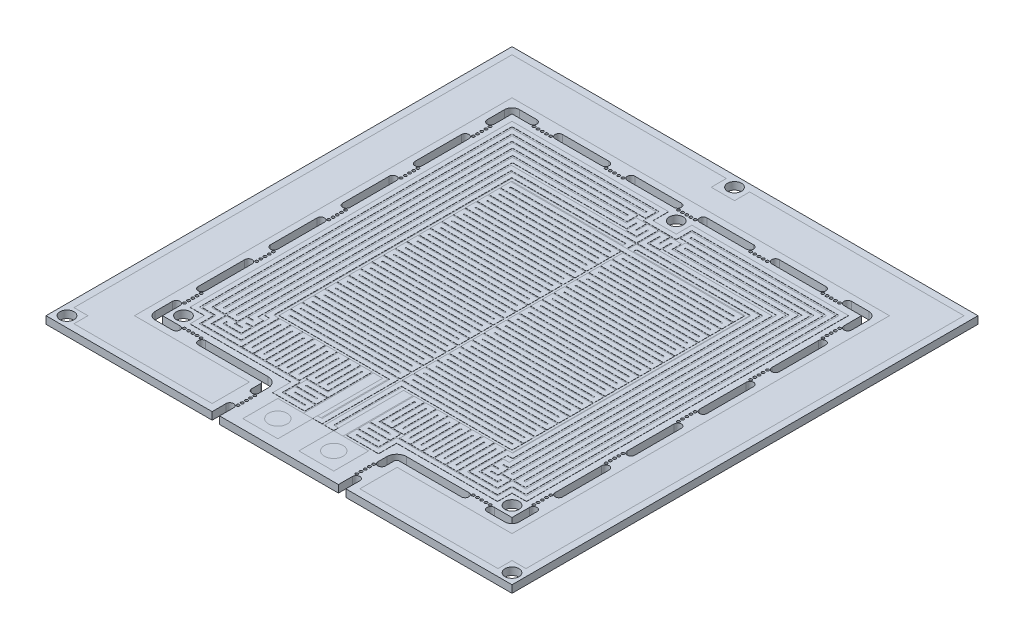
SolidWorks part; units mm, degrees
ref_plane "Front Plane" through (0, 0, 0) normal (0, 0, 1) x (1, 0, 0)
ref_plane "Top Plane" through (0, 0, 0) normal (0, 1, 0) x (1, 0, 0)
ref_plane "Right Plane" through (0, 0, 0) normal (1, 0, 0) x (0, 0, -1)
sketch "Sketch1" plane through (0, 0, 0) normal (0, 1, 0) x (1, 0, 0)
  line L1 (25, 25) -> (-25, 25)
  line L2 (25, 25) -> (25, -25)
  line L3 (25, -25) -> (-25, -25)
  line L4 (-25, 25) -> (-25, -25)
  line L5 (0, -25) -> (0, 25) construction
  line L6 (25, 0) -> (-25, 0) construction
  line L7 (50, 50) -> (-50, 50)
  line L8 (50, 50) -> (50, -50)
  line L9 (50, -50) -> (-50, -50)
  line L10 (-50, 50) -> (-50, -50)
  line L11 (0, -50) -> (0, 50) construction
  line L12 (50, 0) -> (-50, 0) construction
  line L13 (37.5, 37.5) -> (-37.5, 37.5)
  line L14 (37.5, 37.5) -> (37.5, -37.5)
  line L15 (37.5, -37.5) -> (-37.5, -37.5)
  line L16 (-37.5, 37.5) -> (-37.5, -37.5)
  line L17 (0, -37.5) -> (0, 37.5) construction
  line L18 (37.5, 0) -> (-37.5, 0) construction
  point P0 (0, 0)
  point P4 (0, 0)
  point P8 (0, 0)
  dimension "D1" = 100
  dimension "D2" = 50
  dimension "D3" = 75
sketch "Sketch2" plane through (0, 0, 0) normal (0, 1, 0) x (1, 0, 0)
  line L0 (0, 35.25) -> (-35.25, -35.25) construction
  line L1 (0, -50) -> (0, 50) construction
  line L2 (-35.25, -35.25) -> (35.25, -35.25) construction
  line L3 (35.25, -35.25) -> (0, 35.25) construction
  line L4 (0, 47.75) -> (-47.75, -47.75) construction
  line L5 (-47.75, -47.75) -> (47.75, -47.75) construction
  line L6 (47.75, -47.75) -> (0, 47.75) construction
  line L7 (37.5, 37.5) -> (-37.5, 37.5) construction
  line L8 (37.5, -37.5) -> (-37.5, -37.5) construction
  line L9 (-37.5, 37.5) -> (-37.5, -37.5) construction
  line L10 (50, 50) -> (-50, 50) construction
  line L11 (50, -50) -> (-50, -50) construction
  line L12 (-50, 50) -> (-50, -50) construction
  circle A0 centre (-35.25, -35.25) radius 1.5
  circle A1 centre (35.25, -35.25) radius 1.5
  circle A2 centre (0, 35.25) radius 1.5
  circle A3 centre (-47.75, -47.75) radius 1.5
  circle A4 centre (47.75, -47.75) radius 1.5
  circle A5 centre (0, 47.75) radius 1.5
  dimension "D2" = 3
  dimension "D5" = 3
sketch "Sketch3" plane through (0, 0, 0) normal (0, 1, 0) x (1, 0, 0)
  line L0 (50, -50) -> (-50, -50) construction
  line L1 (-2.25, -48) -> (-9.75, -48)
  line L2 (-2.25, -48) -> (-2.25, -40.5)
  line L3 (-2.25, -40.5) -> (-9.75, -40.5)
  line L4 (-9.75, -48) -> (-9.75, -40.5)
  line L5 (-6, -40.5) -> (-6, -48) construction
  line L6 (-2.25, -44.25) -> (-9.75, -44.25) construction
  line L7 (9.75, -48) -> (2.25, -48)
  line L8 (9.75, -48) -> (9.75, -40.5)
  line L9 (9.75, -40.5) -> (2.25, -40.5)
  line L10 (2.25, -48) -> (2.25, -40.5)
  line L11 (6, -40.5) -> (6, -48) construction
  line L12 (9.75, -44.25) -> (2.25, -44.25) construction
  line L15 (0, -50) -> (0, 50) construction
  circle A0 centre (-6, -44.25) radius 2
  circle A1 centre (6, -44.25) radius 2
  point P0 (-6, -44.25)
  point P4 (6, -44.25)
  dimension "D5" = 4
  dimension "D1" = 12
  dimension "D2" = 7.5
  dimension "D3" = 2
  dimension "D4" = 6
sketch "Sketch6" plane through (0, 0, 0) normal (0, 1, 0) x (1, 0, 0)
  line L0 (38.3, -18.25) -> (38.3, -28.25) construction
  line L1 (37.5, -37.5) -> (-37.5, -37.5) construction
  line L4 (12.75, -41.5) -> (12.75, -39.6)
  line L5 (14.85, -37.5) -> (28.25, -37.5)
  line L6 (28.25, -39.1) -> (14.85, -39.1)
  line L7 (14.35, -39.6) -> (14.35, -41.5)
  line L8 (9.75, -48) -> (9.75, -40.5) construction
  line L9 (13.55, -47) -> (13.55, -50) construction
  line L10 (50, -50) -> (-50, -50) construction
  line L11 (14.35, -47) -> (14.35, -50)
  line L12 (12.75, -47) -> (12.75, -50)
  line L13 (13.55, -41.5) -> (13.55, -47) construction
  line L14 (6, -44.25) -> (13.55, -44.25) construction
  line L15 (33.75, -38.3) -> (37.5, -38.3) construction
  line L16 (12.75, -46.05) -> (12.75, -45.15) construction
  line L17 (38.3, -37.5) -> (38.3, -33.75) construction
  line L18 (33.75, -39.1) -> (37.5, -39.1)
  line L19 (39.1, -37.5) -> (39.1, -33.75)
  line L20 (33.75, -37.5) -> (37.5, -37.5)
  line L21 (37.5, -37.5) -> (37.5, -33.75)
  line L22 (37.5, 37.5) -> (37.5, -37.5) construction
  line L23 (12.75, -41.5) -> (12.75, -47) construction
  line L24 (29.2, -37.5) -> (30.1, -37.5) construction
  line L25 (28.25, -38.3) -> (33.75, -38.3) construction
  line L26 (31, -37.5) -> (31, -38.3) construction
  line L27 (39.1, -18.25) -> (39.1, -28.25)
  line L28 (37.5, -18.25) -> (37.5, -28.25)
  line L29 (38.3, -28.25) -> (38.3, -33.75) construction
  line L30 (38.3, -31) -> (37.5, -31) construction
  line L31 (38.3, -2.75) -> (38.3, -12.75) construction
  line L32 (39.1, -2.75) -> (39.1, -12.75)
  line L33 (37.5, -2.75) -> (37.5, -12.75)
  line L34 (0, 0) -> (50, 0) construction
  line L37 (38.3, 18.25) -> (38.3, 28.25) construction
  line L40 (38.3, -18.25) -> (38.3, -2.75) construction
  line L41 (39.1, 18.25) -> (39.1, 28.25)
  line L42 (37.5, 18.25) -> (37.5, 28.25)
  line L43 (38.3, 2.75) -> (38.3, 12.75) construction
  line L44 (39.1, 2.75) -> (39.1, 12.75)
  line L45 (37.5, 2.75) -> (37.5, 12.75)
  line L46 (38.3, 18.25) -> (38.3, 2.75) construction
  line L47 (38.3, 31) -> (37.5, 31) construction
  line L48 (38.3, 28.25) -> (38.3, 33.75) construction
  line L49 (38.3, 37.5) -> (38.3, 33.75) construction
  line L50 (37.5, 37.5) -> (37.5, 33.75)
  line L51 (39.1, 37.5) -> (39.1, 33.75)
  line L52 (31, 37.5) -> (31, 38.3) construction
  line L53 (28.25, 38.3) -> (33.75, 38.3) construction
  line L54 (29.2, 37.5) -> (30.1, 37.5) construction
  line L55 (33.75, 38.3) -> (37.5, 38.3) construction
  line L56 (33.75, 37.5) -> (37.5, 37.5)
  line L57 (33.75, 39.1) -> (37.5, 39.1)
  line L58 (28.25, 38.3) -> (18.25, 38.3) construction
  line L59 (28.25, 37.5) -> (18.25, 37.5)
  line L60 (28.25, 39.1) -> (18.25, 39.1)
  line L61 (12.75, 38.3) -> (2.75, 38.3) construction
  line L62 (12.75, 37.5) -> (2.75, 37.5)
  line L63 (12.75, 39.1) -> (2.75, 39.1)
  line L64 (37.5, 37.5) -> (-37.5, 37.5) construction
  line L65 (37.5, -32.8) -> (37.5, -31.9) construction
  line L66 (37.5, -17.3) -> (37.5, -16.4) construction
  line L67 (37.5, -1.8) -> (37.5, -0.9) construction
  line L68 (37.5, 13.7) -> (37.5, 14.6) construction
  line L69 (37.5, 29.2) -> (37.5, 30.1) construction
  line L70 (37.5, -32.8) -> (37.5, -17.3) construction
  line L71 (13.7, 37.5) -> (14.6, 37.5) construction
  line L72 (32.8, 37.5) -> (17.3, 37.5) construction
  line L73 (0, 0) -> (0, -50) construction
  arc A2 (12.75, -39.6) -> (14.85, -37.5) centre (14.85, -39.6) cw
  arc A3 (28.25, -37.5) -> (28.25, -39.1) centre (28.25, -38.3) cw
  arc A4 (14.85, -39.1) -> (14.35, -39.6) centre (14.85, -39.6) ccw
  arc A5 (14.35, -41.5) -> (12.75, -41.5) centre (13.55, -41.5) cw
  arc A6 (14.35, -47) -> (12.75, -47) centre (13.55, -47) ccw
  arc A7 (12.75, -50) -> (14.35, -50) centre (13.55, -50) ccw
  arc A8 (37.5, -38.3) -> (38.3, -37.5) centre (37.5, -37.5) ccw construction
  arc A9 (37.5, -39.1) -> (39.1, -37.5) centre (37.5, -37.5) ccw
  arc A11 (33.75, -39.1) -> (33.75, -37.5) centre (33.75, -38.3) cw
  arc A12 (39.1, -33.75) -> (37.5, -33.75) centre (38.3, -33.75) ccw
  arc A13 (37.5, -38.3) -> (38.3, -37.5) centre (37.5, -37.5) ccw construction
  arc A14 (37.5, -39.1) -> (39.1, -37.5) centre (37.5, -37.5) ccw construction
  arc A15 (37.5, -37.5) -> (37.5, -37.5) centre (37.5, -37.5) ccw construction
  circle A16 centre (12.75, -46.05) radius 0.3
  circle A18 centre (12.75, -45.15) radius 0.3
  circle A19 centre (12.75, -44.25) radius 0.3
  circle A20 centre (12.75, -43.35) radius 0.3
  circle A21 centre (12.75, -42.45) radius 0.3
  circle A22 centre (29.2, -37.5) radius 0.3
  circle A23 centre (30.1, -37.5) radius 0.3
  circle A24 centre (31, -37.5) radius 0.3
  circle A25 centre (31.9, -37.5) radius 0.3
  circle A26 centre (32.8, -37.5) radius 0.3
  arc A27 (39.1, -18.25) -> (37.5, -18.25) centre (38.3, -18.25) ccw
  arc A28 (37.5, -28.25) -> (39.1, -28.25) centre (38.3, -28.25) ccw
  arc A29 (39.1, -2.75) -> (37.5, -2.75) centre (38.3, -2.75) ccw
  arc A30 (37.5, -12.75) -> (39.1, -12.75) centre (38.3, -12.75) ccw
  arc A35 (39.1, 18.25) -> (37.5, 18.25) centre (38.3, 18.25) cw
  arc A36 (37.5, 28.25) -> (39.1, 28.25) centre (38.3, 28.25) cw
  arc A37 (39.1, 2.75) -> (37.5, 2.75) centre (38.3, 2.75) cw
  arc A38 (37.5, 12.75) -> (39.1, 12.75) centre (38.3, 12.75) cw
  arc A39 (37.5, 38.3) -> (38.3, 37.5) centre (37.5, 37.5) cw construction
  arc A40 (39.1, 33.75) -> (37.5, 33.75) centre (38.3, 33.75) cw
  arc A41 (37.5, 39.1) -> (39.1, 37.5) centre (37.5, 37.5) cw
  circle A42 centre (32.8, 37.5) radius 0.3
  circle A43 centre (31.9, 37.5) radius 0.3
  circle A44 centre (31, 37.5) radius 0.3
  circle A45 centre (30.1, 37.5) radius 0.3
  circle A46 centre (29.2, 37.5) radius 0.3
  arc A47 (33.75, 39.1) -> (33.75, 37.5) centre (33.75, 38.3) ccw
  arc A48 (28.25, 37.5) -> (28.25, 39.1) centre (28.25, 38.3) ccw
  arc A49 (18.25, 39.1) -> (18.25, 37.5) centre (18.25, 38.3) ccw
  arc A50 (12.75, 37.5) -> (12.75, 39.1) centre (12.75, 38.3) ccw
  arc A51 (2.75, 39.1) -> (2.75, 37.5) centre (2.75, 38.3) ccw
  circle A52 centre (37.5, -32.8) radius 0.3
  circle A53 centre (37.5, -31.9) radius 0.3
  circle A54 centre (37.5, -31) radius 0.3
  circle A55 centre (37.5, -30.1) radius 0.3
  circle A56 centre (37.5, -29.2) radius 0.3
  circle A57 centre (37.5, -17.3) radius 0.3
  circle A58 centre (37.5, -16.4) radius 0.3
  circle A59 centre (37.5, -15.5) radius 0.3
  circle A60 centre (37.5, -14.6) radius 0.3
  circle A61 centre (37.5, -13.7) radius 0.3
  circle A62 centre (37.5, -1.8) radius 0.3
  circle A63 centre (37.5, -0.9) radius 0.3
  circle A64 centre (37.5, 0) radius 0.3
  circle A65 centre (37.5, 0.9) radius 0.3
  circle A66 centre (37.5, 1.8) radius 0.3
  circle A67 centre (37.5, 13.7) radius 0.3
  circle A68 centre (37.5, 14.6) radius 0.3
  circle A69 centre (37.5, 15.5) radius 0.3
  circle A70 centre (37.5, 16.4) radius 0.3
  circle A71 centre (37.5, 17.3) radius 0.3
  circle A72 centre (37.5, 29.2) radius 0.3
  circle A73 centre (37.5, 30.1) radius 0.3
  circle A74 centre (37.5, 31) radius 0.3
  circle A75 centre (37.5, 31.9) radius 0.3
  circle A76 centre (37.5, 32.8) radius 0.3
  circle A77 centre (17.3, 37.5) radius 0.3
  circle A78 centre (16.4, 37.5) radius 0.3
  circle A79 centre (15.5, 37.5) radius 0.3
  circle A80 centre (14.6, 37.5) radius 0.3
  circle A81 centre (13.7, 37.5) radius 0.3
  point P0 (31, -37.9)
  point P5 (38.3, -23.25)
  point P11 (13.55, -48.5)
  point P88 (38.3, -7.75)
  point P95 (38.3, 23.25)
  point P102 (38.3, 7.75)
  point P122 (23.25, 38.3)
  point P145 (7.75, 38.3)
  dimension "D2" = 0.5
  dimension "D8" = 0.9
  dimension "D5" = 0.6
  dimension "D7" = 5
  dimension "D10" = 0.6
  dimension "D20" = 0.6
  dimension "D1" = 1.6
  dimension "D3" = 3
  dimension "D4" = 5.5
  dimension "D6" = 1.6
  dimension "D9" = 5.5
  dimension "D12" = 0.9
  dimension "D13" = 4.25
  dimension "D14" = 5.5
  dimension "D15" = 4.25
  dimension "D16" = 10
  dimension "D18" = 15.5
  dimension "D19" = 5.5
  dimension "D22" = 0.9
  dimension "D24" = 15.5
  dimension "D26" = 15.5
  dimension "D11" = 5
  dimension "D17" = 2
  dimension "D21" = 5
  dimension "D23" = 5
  dimension "D25" = 2
extrude "Boss-Extrude1" add sketch "Sketch1" against normal blind 1.6 contours L10 L9 L8 L7
extrude "Cut-Extrude1" cut sketch "Sketch2" against normal blind 1.6
extrude "Cut-Extrude2" cut sketch "Sketch6" against normal blind 1.6 contours L12 A7 L11 A6 | A16 | A18 | A19 | A20 | A21 | A5 L7 A4 L6 A3 L5 A2 L4 | L19 A12 L21 L20 A11 L18 A9 | A26 | A25 | A24 | A23 | A22 | L28 A28 L27 A27 | L33 A30 L32 A29 | A52 | A53 | A54 | A55 | A56 | A66 | A65 | A64 | A63 | A62 | A57 | A58 | A59 | A60 | A61 | A38 L45 A37 L44 | A36 L42 A35 L41 | L57 A47 L56 L50 A40 L51 A41 | A67 | A68 | A69 | A70 | A71 | A72 | A73 | A74 | A75 | A76 | L60 A49 L59 A48 | A45 | A44 | A43 | A42 | A77 | A78 | A79 | A80 | A81 | L63 A51 L62 A50 | A46
mirror "Mirror1" about plane through (0, 0, 0) normal (1, 0, 0) of "Cut-Extrude2"
sketch "Sketch7" plane through (0, 0, 0) normal (0, 1, 0) x (1, 0, 0)
  line L0 (-2.75, 37.5) -> (2.75, 37.5) construction
  line L1 (1.8, 37.5) -> (0.9, 37.5) construction
  circle A0 centre (1.8, 37.5) radius 0.3
  circle A1 centre (0.9, 37.5) radius 0.3
  circle A2 centre (0, 37.5) radius 0.3
  circle A3 centre (-0.9, 37.5) radius 0.3
  circle A4 centre (-1.8, 37.5) radius 0.3
  dimension "D1" = 0.6
  dimension "D3" = 0.9
  dimension "D2" = 5
extrude "Cut-Extrude3" cut sketch "Sketch7" against normal blind 1.6
sketch "Sketch8" plane through (0, 0, 0) normal (0, 1, 0) x (1, 0, 0)
  line L0 (1.3628, 31.4839) -> (5.2355, 31.4839)
  line L1 (5.2355, 31.4839) -> (5.2355, 35.5)
  line L2 (5.2355, 35.5) -> (35.5, 35.5)
  line L3 (35.5, 35.5) -> (35.5, -32.5)
  line L4 (35.5, -32.5) -> (34, -32.5)
  line L5 (34, -32.5) -> (34, 34)
  line L6 (34, 34) -> (7.2968, 34)
  line L7 (7.2968, 34) -> (7.2968, 32.5)
  line L8 (7.2968, 32.5) -> (32.5, 32.5)
  line L9 (32.5, 32.5) -> (32.5, -36)
  line L10 (32.5, -36) -> (10.3613, -36)
  line L11 (10.3613, -36) -> (10.3613, -34.5)
  line L12 (10.3613, -34.5) -> (31, -34.5)
  line L13 (31, -34.5) -> (31, 31)
  line L14 (31, 31) -> (10.9302, 31)
  line L15 (10.9302, 31) -> (10.9302, 25.9634)
  line L16 (10.9302, 25.9634) -> (27.2604, 25.9634)
  line L17 (27.2604, 25.9634) -> (27.2604, -17.6224)
  line L18 (37.5, 37.5) -> (37.5, -37.5) construction
  line L19 (37.5, 37.5) -> (-37.5, 37.5) construction
  line L20 (37.5, -37.5) -> (-37.5, -37.5) construction
  dimension "D1" = 2
  dimension "D2" = 2
  dimension "D3" = 1.5
  dimension "D4" = 1.5
  dimension "D5" = 1.5
  dimension "D6" = 1.5
  dimension "D7" = 1.5
  dimension "D8" = 5
  dimension "D9" = 1.5
  dimension "D10" = 1.5
  dimension "D11" = 1.5
sketch "Sketch9" plane through (0, 0, 0) normal (0, 1, 0) x (1, 0, 0)
  line L0 (-48.5, -45.5) -> (-45.5, -45.5)
  line L1 (-45.5, -45.5) -> (-45.5, -48.5)
  line L2 (-45.5, -48.5) -> (-15.85, -48.5)
  line L3 (-15.85, -48.5) -> (-15.85, -40.5)
  line L4 (-15.85, -40.5) -> (-40.5, -40.5)
  line L5 (-40.5, -40.5) -> (-40.5, 40.5)
  line L6 (-40.5, 40.5) -> (40.5, 40.5)
  line L7 (0, -50) -> (0, 50) construction
  line L9 (2.5, 45.25) -> (-2.5, 45.25)
  line L10 (-2.5, 45.25) -> (-2.5, 48.5)
  line L11 (-2.5, 48.5) -> (-48.5, 48.5)
  line L12 (-48.5, 48.5) -> (-48.5, -45.5)
  line L13 (-14.35, -50) -> (-50, -50) construction
  line L14 (-50, 50) -> (-50, -50) construction
  line L16 (-14.35, -39.6) -> (-14.35, -41.5) construction
  line L18 (50, 50) -> (-50, 50) construction
  line L19 (-2.25, -40.5) -> (-9.75, -40.5) construction
  line L20 (-4.25, -40.5) -> (-2.25, -40.5)
  line L21 (-4.25, -40.5) -> (-4.25, -25.5)
  line L22 (-4.25, -25.5) -> (-2.25, -25.5)
  line L23 (-2.25, -40.5) -> (-2.25, -25.5)
  line L24 (-3.25, -25.5) -> (-3.25, -40.5) construction
  line L25 (-4.25, -33) -> (-2.25, -33) construction
  line L26 (-4.5, -25.5) -> (-25.5, -25.5)
  line L27 (25, 25) -> (-25, 25)
  line L28 (25, 25) -> (25, -25)
  line L29 (25, -25) -> (-25, -25)
  line L30 (-25, 25) -> (-25, -25)
  line L31 (0, -25) -> (0, 25) construction
  line L32 (25, 0) -> (-25, 0) construction
  line L33 (-25.5, -25.5) -> (-25.5, 25.5)
  line L34 (-2.5, 36.1) -> (-36.1, 36.1)
  line L35 (-36.1, 36.1) -> (-36.1, -33)
  line L36 (-36.1, -33) -> (-33, -33)
  line L37 (-33, -33) -> (-33, -36.1)
  line L38 (-33, -36.1) -> (-11.35, -36.1)
  line L39 (-11.35, -36.1) -> (-11.35, -40)
  line L40 (-11.35, -40) -> (-4.5, -40)
  line L41 (-4.5, -40) -> (-4.5, -25.5)
  line L42 (-14.85, -37.5) -> (-28.25, -37.5) construction
  line L43 (-37.5, -18.25) -> (-37.5, -28.25) construction
  line L44 (-12.75, -41.5) -> (-12.75, -39.6) construction
  line L45 (-25.5, 25.5) -> (25.5, 25.5)
  line L46 (-2.5, 36.1) -> (-2.5, 32.75)
  line L47 (-2.5, 32.75) -> (2.5, 32.75)
  line L48 (-12.75, 37.5) -> (-2.75, 37.5) construction
  line L49 (25.5, -25.5) -> (25.5, 25.5)
  line L50 (4.5, -25.5) -> (25.5, -25.5)
  line L51 (4.5, -40) -> (4.5, -25.5)
  line L52 (11.35, -40) -> (4.5, -40)
  line L53 (11.35, -36.1) -> (11.35, -40)
  line L54 (33, -36.1) -> (11.35, -36.1)
  line L55 (33, -33) -> (33, -36.1)
  line L56 (36.1, -33) -> (33, -33)
  line L57 (36.1, 36.1) -> (36.1, -33)
  line L58 (2.5, 36.1) -> (36.1, 36.1)
  line L59 (2.5, 36.1) -> (2.5, 32.75)
  line L60 (-28.25, 39.1) -> (-18.25, 39.1) construction
  line L61 (40.5, -40.5) -> (40.5, 40.5)
  line L62 (15.85, -40.5) -> (40.5, -40.5)
  line L63 (15.85, -48.5) -> (15.85, -40.5)
  line L64 (45.5, -48.5) -> (15.85, -48.5)
  line L65 (45.5, -45.5) -> (45.5, -48.5)
  line L66 (48.5, -45.5) -> (45.5, -45.5)
  line L67 (48.5, 48.5) -> (48.5, -45.5)
  line L68 (2.5, 48.5) -> (48.5, 48.5)
  line L69 (2.5, 45.25) -> (2.5, 48.5)
  line L70 (4.25, -40.5) -> (2.25, -40.5)
  line L71 (4.25, -40.5) -> (4.25, -25.5)
  line L72 (4.25, -25.5) -> (2.25, -25.5)
  line L73 (2.25, -40.5) -> (2.25, -25.5)
  line L74 (-1.5, -25) -> (-1.5, -40.5)
  line L75 (-1.5, -40.5) -> (1.5, -40.5)
  line L76 (1.5, -40.5) -> (1.5, -25)
  line L77 (0, -40.5) -> (0, -25) construction
  circle A0 centre (-47.75, -47.75) radius 1.5 construction
  circle A1 centre (0, 47.75) radius 1.5 construction
  circle A2 centre (-35.25, -35.25) radius 1.5 construction
  circle A3 centre (0, 35.25) radius 1.5 construction
  point P20 (-14.35, -40.55)
  point P33 (0, 0)
  point P65 (-7.75, 37.5)
  point P67 (0, 25.5)
  point P78 (0, 32.75)
  point P81 (0, 40.5)
  point P90 (0, 45.25)
  point P135 (-3.25, -33)
  dimension "D6" = 2.25
  dimension "D10" = 2.5
  dimension "D11" = 2.5
  dimension "D14" = 2.25
  dimension "D15" = 2.25
  dimension "D23" = 2.5
  dimension "D25" = 2.5
  dimension "D1" = 1.5
  dimension "D2" = 1.5
  dimension "D3" = 8
  dimension "D4" = 8
  dimension "D5" = 1.5
  dimension "D7" = 2.25
  dimension "D8" = 1.5
  dimension "D9" = 1.4
  dimension "D12" = 2
  dimension "D13" = 50
  dimension "D16" = 1.4
  dimension "D17" = 1.4
  dimension "D18" = 1.4
  dimension "D19" = 0.25
  dimension "D20" = 0.5
  dimension "D21" = 0.5
  dimension "D22" = 0.5
  dimension "D24" = 1.4
  dimension "D26" = 0.5
  dimension "D27" = 3
split line "Split Line1"
split line "Split Line2"
sketch "Sketch10" plane through (0, 0, 0) normal (0, 1, 0) x (1, 0, 0)
  line L0 (0, -40.5) -> (0, 0) construction
  line L1 (1.5, -40.5) -> (-1.5, -40.5) construction
  line L2 (0.75, -40) -> (0.75, -24.5)
  line L3 (0.75, 20.5) -> (0.75, 19.25)
  line L4 (0.75, 19.25) -> (24.5, 19.25)
  line L5 (24.5, 18) -> (0.75, 18)
  line L6 (24.5, 19.25) -> (24.5, 18)
  line L7 (2.25, -40.5) -> (2.25, -25.5) construction
  line L8 (0.75, -40) -> (2.25, -40)
  line L9 (25, 25) -> (25, -25) construction
  line L10 (25, -25) -> (1.5, -25) construction
  line L12 (24.5, 23) -> (24.5, 24.25)
  line L13 (24.5, 24.25) -> (0, 24.25)
  line L14 (24.5, 23) -> (0.75, 23)
  line L15 (0.75, 23) -> (0.75, 21.75)
  line L16 (0.75, 21.75) -> (24.5, 21.75)
  line L17 (24.5, 21.75) -> (24.5, 20.5)
  line L18 (24.5, 20.5) -> (0.75, 20.5)
  line L21 (0.75, 18) -> (0.75, 16.75)
  line L22 (0.75, 16.75) -> (24.5, 16.75)
  line L23 (24.5, 15.5) -> (0.75, 15.5)
  line L24 (24.5, 16.75) -> (24.5, 15.5)
  line L25 (0.75, 15.5) -> (0.75, 14.25)
  line L26 (0.75, 14.25) -> (24.5, 14.25)
  line L27 (24.5, 13) -> (0.75, 13)
  line L28 (24.5, 14.25) -> (24.5, 13)
  line L29 (0.75, 13) -> (0.75, 11.75)
  line L30 (0.75, 11.75) -> (24.5, 11.75)
  line L31 (24.5, 10.5) -> (0.75, 10.5)
  line L32 (24.5, 11.75) -> (24.5, 10.5)
  line L33 (0.75, 10.5) -> (0.75, 9.25)
  line L34 (0.75, 9.25) -> (24.5, 9.25)
  line L35 (24.5, 8) -> (0.75, 8)
  line L36 (24.5, 9.25) -> (24.5, 8)
  line L37 (0.75, 8) -> (0.75, 6.75)
  line L38 (0.75, 6.75) -> (24.5, 6.75)
  line L39 (24.5, 5.5) -> (0.75, 5.5)
  line L40 (24.5, 6.75) -> (24.5, 5.5)
  line L41 (0.75, 5.5) -> (0.75, 4.25)
  line L42 (0.75, 4.25) -> (24.5, 4.25)
  line L43 (24.5, 3) -> (0.75, 3)
  line L44 (24.5, 4.25) -> (24.5, 3)
  line L45 (0.75, 3) -> (0.75, 1.75)
  line L46 (0.75, 1.75) -> (24.5, 1.75)
  line L47 (24.5, 0.5) -> (0.75, 0.5)
  line L48 (24.5, 1.75) -> (24.5, 0.5)
  line L49 (0.75, 0.5) -> (0.75, -0.75)
  line L50 (0.75, -0.75) -> (24.5, -0.75)
  line L51 (24.5, -2) -> (0.75, -2)
  line L52 (24.5, -0.75) -> (24.5, -2)
  line L53 (0.75, -2) -> (0.75, -3.25)
  line L54 (0.75, -3.25) -> (24.5, -3.25)
  line L55 (24.5, -4.5) -> (0.75, -4.5)
  line L56 (24.5, -3.25) -> (24.5, -4.5)
  line L57 (0.75, -4.5) -> (0.75, -5.75)
  line L58 (0.75, -5.75) -> (24.5, -5.75)
  line L59 (24.5, -7) -> (0.75, -7)
  line L60 (24.5, -5.75) -> (24.5, -7)
  line L61 (0.75, -7) -> (0.75, -8.25)
  line L62 (0.75, -8.25) -> (24.5, -8.25)
  line L63 (24.5, -9.5) -> (0.75, -9.5)
  line L64 (24.5, -8.25) -> (24.5, -9.5)
  line L65 (0.75, -9.5) -> (0.75, -10.75)
  line L66 (0.75, -10.75) -> (24.5, -10.75)
  line L67 (24.5, -12) -> (0.75, -12)
  line L68 (24.5, -10.75) -> (24.5, -12)
  line L69 (0.75, -12) -> (0.75, -13.25)
  line L70 (0.75, -13.25) -> (24.5, -13.25)
  line L71 (24.5, -14.5) -> (0.75, -14.5)
  line L72 (24.5, -13.25) -> (24.5, -14.5)
  line L73 (0.75, -14.5) -> (0.75, -15.75)
  line L74 (0.75, -15.75) -> (24.5, -15.75)
  line L75 (24.5, -17) -> (0.75, -17)
  line L76 (24.5, -15.75) -> (24.5, -17)
  line L77 (0.75, -17) -> (0.75, -18.25)
  line L78 (0.75, -18.25) -> (24.5, -18.25)
  line L79 (24.5, -19.5) -> (0.75, -19.5)
  line L80 (24.5, -18.25) -> (24.5, -19.5)
  line L81 (0.75, -19.5) -> (0.75, -20.75)
  line L82 (0.75, -20.75) -> (24.5, -20.75)
  line L83 (24.5, -22) -> (0.75, -22)
  line L84 (24.5, -20.75) -> (24.5, -22)
  line L85 (0.75, -22) -> (0.75, -23.25)
  line L86 (0.75, -23.25) -> (24.5, -23.25)
  line L87 (24.5, -24.5) -> (0.75, -24.5)
  line L88 (24.5, -23.25) -> (24.5, -24.5)
  line L89 (0.75, 23) -> (0.75, 20.5) construction
  dimension "D1" = 0.75
  dimension "D2" = 0.5
  dimension "D3" = 0.5
  dimension "D4" = 0.5
  dimension "D5" = 1.25
  dimension "D6" = 1.25
  dimension "D8" = 19
extrude "Extrude-Thin1" add sketch "Sketch10" along normal blind 0.035 separate body thin thin type mid plane wall 1
mirror "Mirror3" about plane through (0, 0, 0) normal (1, 0, 0) of bodies 108
sketch "Sketch12" plane through (0, 0, 0) normal (0, 1, 0) x (1, 0, 0)
  line L0 (0.625, 24.75) -> (0.625, 26.1)
  line L1 (-25, 24.75) -> (25, 24.75) construction
  line L2 (0.625, 26.1) -> (26.15, 26.1)
  line L3 (0, 32.25) -> (3, 32.25)
  line L4 (3, 32.25) -> (3, 35.6)
  line L5 (3, 35.6) -> (35.6, 35.6)
  line L6 (35.6, 35.6) -> (35.6, -32.5)
  line L7 (35.6, -32.5) -> (32.5, -32.5)
  line L8 (32.5, -32.5) -> (32.5, -35.6)
  line L9 (32.5, -35.6) -> (10.85, -35.6)
  line L10 (10.85, -35.6) -> (10.85, -39.5)
  line L11 (10.85, -39.5) -> (5, -39.5)
  line L12 (5, -39.5) -> (5, -38.25)
  line L13 (5, -38.25) -> (9.6, -38.25)
  line L14 (9.6, -38.25) -> (9.6, -37)
  line L15 (9.6, -37) -> (5, -37)
  line L16 (5, -37) -> (5, -35.75)
  line L17 (5, -35.75) -> (9.6, -35.75)
  line L18 (11.35, -36.1) -> (11.35, -40) construction
  line L19 (11.35, -40) -> (4.5, -40) construction
  line L20 (9.6, -35.75) -> (9.6, -34.5)
  line L21 (9.6, -34.5) -> (5, -34.5)
  line L22 (4.5, -40) -> (4.5, -25.5) construction
  line L23 (33, -33) -> (33, -36.1) construction
  line L24 (36.1, -33) -> (33, -33) construction
  line L25 (36.1, 36.1) -> (36.1, -33) construction
  line L26 (33, -36.1) -> (11.35, -36.1) construction
  line L27 (2.5, 36.1) -> (36.1, 36.1) construction
  line L28 (2.5, 32.75) -> (2.5, 36.1) construction
  line L29 (-2.5, 32.75) -> (2.5, 32.75) construction
  line L30 (0, 32.25) -> (0, 35.25) construction
  line L31 (25.5, 25.5) -> (-25.5, 25.5) construction
  line L32 (5, -34.5) -> (5, -26)
  line L33 (5, -26) -> (6.25, -26)
  line L34 (6.25, -26) -> (6.25, -33.25)
  line L35 (6.25, -33.25) -> (7.5, -33.25)
  line L36 (7.5, -33.25) -> (7.5, -26)
  line L37 (7.5, -26) -> (8.75, -26)
  line L38 (8.75, -26) -> (8.75, -33.25)
  line L39 (8.75, -33.25) -> (10, -33.25)
  line L40 (10, -33.25) -> (10, -26)
  line L41 (10, -26) -> (11.25, -26)
  line L42 (11.25, -26) -> (11.25, -34.35)
  line L43 (11.25, -34.35) -> (12.5, -34.35)
  line L44 (12.5, -34.35) -> (12.5, -26)
  line L45 (4.5, -25.5) -> (25.5, -25.5) construction
  line L46 (12.5, -26) -> (13.75, -26)
  line L47 (13.75, -26) -> (13.75, -34.35)
  line L48 (13.75, -34.35) -> (15, -34.35)
  line L49 (15, -34.35) -> (15, -26)
  line L50 (15, -26) -> (16.25, -26)
  line L51 (16.25, -26) -> (16.25, -34.35)
  line L52 (16.25, -34.35) -> (17.5, -34.35)
  line L53 (17.5, -34.35) -> (17.5, -26)
  line L54 (17.5, -26) -> (18.75, -26)
  line L55 (18.75, -26) -> (18.75, -34.35)
  line L56 (18.75, -34.35) -> (20, -34.35)
  line L57 (20, -34.35) -> (20, -26)
  line L58 (20, -26) -> (21.25, -26)
  line L59 (21.25, -26) -> (21.25, -34.35)
  line L60 (21.25, -34.35) -> (22.5, -34.35)
  line L61 (22.5, -34.35) -> (22.5, -26)
  line L62 (22.5, -26) -> (23.75, -26)
  line L63 (23.75, -26) -> (23.75, -34.35)
  line L64 (23.75, -34.35) -> (31.25, -34.35)
  line L65 (26.25, -31.85) -> (26.25, -30.6)
  line L66 (26.25, -30.6) -> (27.6, -30.6)
  line L67 (27.6, -30.6) -> (27.6, -29.35)
  line L68 (27.6, -29.35) -> (26.25, -29.35)
  line L69 (26.25, -29.35) -> (26.25, -28.1)
  line L70 (26.25, -28.1) -> (27.5, -28.1)
  line L71 (27.5, -28.1) -> (27.5, -26)
  line L72 (30, -31.85) -> (30, -31.25)
  line L73 (31.25, -34.35) -> (31.25, -31.25)
  line L74 (30, -31.25) -> (28.75, -31.25)
  line L75 (26.15, 26.1) -> (26.15, -26)
  line L76 (4.375, 28.95) -> (4.375, 31)
  line L78 (4.25, 32.9) -> (4.25, 34.25)
  line L79 (4.25, 34.25) -> (34.25, 34.25)
  line L80 (34.25, 34.25) -> (34.25, -31.25)
  line L82 (32.9, -30) -> (32.9, 32.9)
  line L83 (32.9, 32.9) -> (4.25, 32.9)
  line L85 (28.75, -31.25) -> (28.75, -31.85)
  line L86 (31.25, -31.25) -> (34.25, -31.25)
  line L89 (32.9, -30) -> (31.55, -30)
  line L90 (31.55, -30) -> (31.55, 31.65)
  line L91 (31.55, 31.65) -> (5.625, 31.65)
  line L92 (5.625, 31.65) -> (5.625, 30.3)
  line L93 (27.5, 27.35) -> (27.5, -26)
  line L94 (0.625, 31) -> (1.875, 31)
  line L95 (3.125, 28.6) -> (3.125, 31)
  line L96 (3.125, 31) -> (4.375, 31)
  line L97 (5.625, 30.3) -> (30.2, 30.3)
  line L98 (30.2, 30.3) -> (30.2, -30)
  line L99 (30.2, -30) -> (28.85, -30)
  line L100 (28.85, -30) -> (28.85, 28.95)
  line L101 (1.875, 31) -> (1.875, 28.6)
  line L102 (26.15, -26) -> (25, -26)
  line L103 (25, -26) -> (25, -33.1)
  line L104 (25, -33.1) -> (30, -33.1)
  line L105 (30, -33.1) -> (30, -31.85)
  line L106 (28.75, -31.85) -> (26.25, -31.85)
  line L107 (1.875, 28.6) -> (3.125, 28.6)
  line L109 (0.625, 27.35) -> (0.625, 31)
  line L110 (4.375, 28.95) -> (28.85, 28.95)
  line L111 (0.625, 27.35) -> (27.5, 27.35)
  point P108 (4.2535, 30.4274)
  point P114 (4.375, 28.95)
  point P122 (4.25, 28.4429)
  point P123 (0, 0)
  dimension "D1" = 1.25
  dimension "D2" = 0.5
  dimension "D3" = 0.5
  dimension "D4" = 0.5
  dimension "D5" = 1.25
  dimension "D6" = 0.5
  dimension "D7" = 0.5
  dimension "D8" = 0.5
  dimension "D9" = 0.5
  dimension "D10" = 0.5
  dimension "D11" = 0.5
  dimension "D12" = 0.5
  dimension "D13" = 0.6
  dimension "D14" = 1.25
  dimension "D15" = 0.5
  dimension "D16" = 1.25
  dimension "D17" = 1.25
  dimension "D18" = 1.25
  dimension "D19" = 1.35
  dimension "D20" = 1.25
  dimension "D21" = 1.25
  dimension "D22" = 1.25
  dimension "D23" = 1.25
  dimension "D24" = 1.25
  dimension "D25" = 1.25
  dimension "D26" = 1.25
  dimension "D27" = 1.25
  dimension "D28" = 1.25
  dimension "D29" = 1.25
  dimension "D30" = 1.25
  dimension "D31" = 1.25
  dimension "D32" = 1.25
  dimension "D33" = 1.25
  dimension "D34" = 1.25
  dimension "D35" = 1.25
  dimension "D36" = 1.25
  dimension "D37" = 1.25
  dimension "D38" = 1.25
extrude "Extrude-Thin2" add sketch "Sketch12" along normal blind 0.035 separate body thin thin type mid plane wall 1
mirror "Mirror4" about plane through (0, 0, 0) normal (1, 0, 0) of bodies 110
